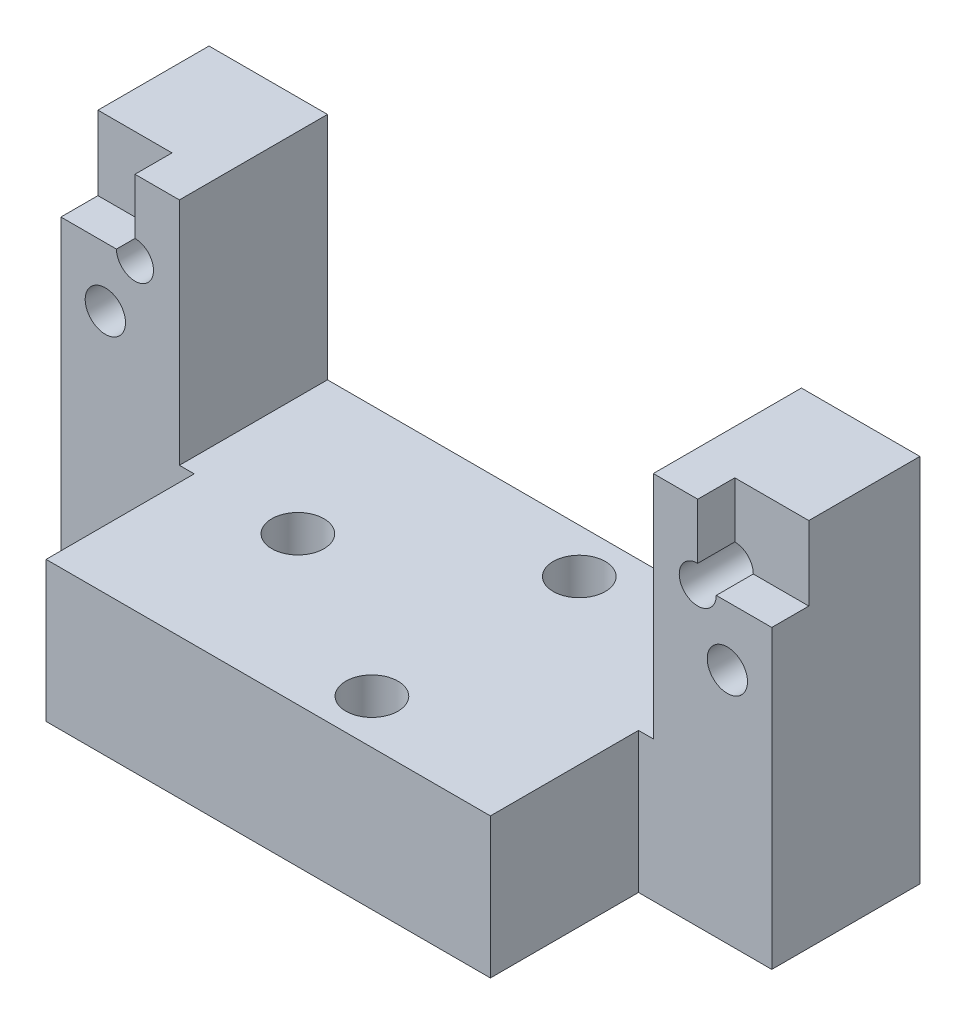
SolidWorks part; units mm, degrees
material "6061 Alloy"
ref_plane "Front Plane" through (0, 0, 0) normal (0, 0, 1) x (1, 0, 0)
ref_plane "Top Plane" through (0, 0, 0) normal (0, 1, 0) x (1, 0, 0)
ref_plane "Right Plane" through (0, 0, 0) normal (1, 0, 0) x (0, 0, -1)
sketch "Sketch1" plane through (0, 0, 0) normal (0, 0, 1) x (1, 0, 0)
  line L1 (-30.48, 15.875) -> (30.48, 15.875)
  line L2 (-30.48, 15.875) -> (-30.48, -15.875)
  line L3 (-30.48, -15.875) -> (30.48, -15.875)
  line L4 (30.48, 15.875) -> (30.48, -15.875)
  dimension "D1" = 30.48
  dimension "D2" = 30.48
  dimension "D3" = 15.875
  dimension "D4" = 15.875
extrude "Boss-Extrude1" add sketch "Sketch1" along normal mid plane 25.4
sketch "Sketch4" plane through (0, 0, 12.7) normal (0, 0, 1) x (1, 0, 0)
  line L0 (30.48, 15.875) -> (-30.48, 15.875) construction
  line L1 (-20.32, 15.875) -> (20.32, 15.875)
  line L2 (-20.32, 15.875) -> (-20.32, -3.8354)
  line L3 (-20.32, -3.8354) -> (20.32, -3.8354)
  line L4 (20.32, 15.875) -> (20.32, -3.8354)
  dimension "D1" = 40.64
  dimension "D2" = 20.32
  dimension "D3" = 19.7104
extrude "Cut-Extrude2" cut sketch "Sketch4" against normal up to next
sketch "Sketch5" plane through (0, 0, 12.7) normal (0, 0, 1) x (1, 0, 0)
  line L0 (-30.48, -15.875) -> (30.48, -15.875) construction
  line L1 (30.48, 15.875) -> (19.05, 15.875)
  line L2 (30.48, 15.875) -> (30.48, -15.875)
  line L3 (30.48, -15.875) -> (19.05, -15.875)
  line L4 (19.05, 15.875) -> (19.05, -15.875)
  dimension "D1" = 11.43
  dimension "D2" = 31.75
extrude "Cut-Extrude3" cut sketch "Sketch5" against normal blind 12.7
mirror "Mirror2" about plane through (0, 0, 0) normal (1, 0, 0) of "Cut-Extrude3"
sketch "Sketch6" plane through (0, 0, 0) normal (0, 0, 1) x (1, 0, 0)
  line L1 (30.48, 15.875) -> (24.13, 15.875)
  line L2 (30.48, 15.875) -> (30.48, 9.525)
  line L3 (30.48, 9.525) -> (24.13, 9.525)
  line L4 (24.13, 15.875) -> (24.13, 9.525)
  dimension "D1" = 6.35
  dimension "D2" = 6.35
extrude "Cut-Extrude4" cut sketch "Sketch6" against normal blind 3.175
sketch "Sketch7" plane through (0, 0, 0) normal (0, 0, 1) x (1, 0, 0)
  circle A0 centre (24.13, 9.525) radius 1.5875
extrude "Cut-Extrude5" cut sketch "Sketch7" against normal blind 6.35
hole_wizard "#8-32 Tapped Hole1" positions "Sketch9" profile "Sketch8" tap size "#8-32" standard "ANSI Inch" end condition up to next
sketch "Sketch9" plane through (0, 0, 0) normal (0, 0, 1) x (1, 0, 0)
  line L0 (30.48, -15.875) -> (30.48, 9.525) construction
  line L1 (24.13, 15.875) -> (20.32, 15.875) construction
  point P0 (26.67, 4.445)
  dimension "D1" = 3.81
  dimension "D2" = 11.43
sketch "Sketch8" plane through (26.67, 4.445, 0) normal (1, 0, 0) x (0, -1, 0)
  line L0 (0, 0) -> (0, 12.701)
  line L1 (0, 12.701) -> (1.7272, 12.701)
  line L2 (1.7272, 12.701) -> (1.7272, 0)
  line L5 (1.7272, 0) -> (0, 0)
  line L11 (0, -6.35) -> (0, 107.95) construction
  dimension "Thru Tap Drill Dia." = 3.4544
  dimension "Thru Tap Drill Depth" = 12.701
cosmetic thread "Hole Thread1" parameters "D2"=4.1656
sketch "Sketch10" plane through (0, -3.8354, 0) normal (0, 1, 0) x (1, 0, 0)
  circle A0 centre (5.08, 8.89) radius 2.2352
  circle A1 centre (5.08, -8.89) radius 2.2352
  circle A2 centre (-10.16, 0) radius 2.2352
  dimension "D1" = 5.08
  dimension "D2" = 8.89
  dimension "D3" = 8.89
  dimension "D4" = 10.16
extrude "Cut-Extrude6" cut sketch "Sketch10" against normal up to next
sketch "Sketch11" plane through (0, -3.8354, 0) normal (0, 1, 0) x (1, 0, 0)
  circle A0 centre (0, 0) radius 10.16
mirror "Mirror3" about plane through (0, 0, 0) normal (1, 0, 0) of "#8-32 Tapped Hole1", "Cut-Extrude5", "Cut-Extrude4"
